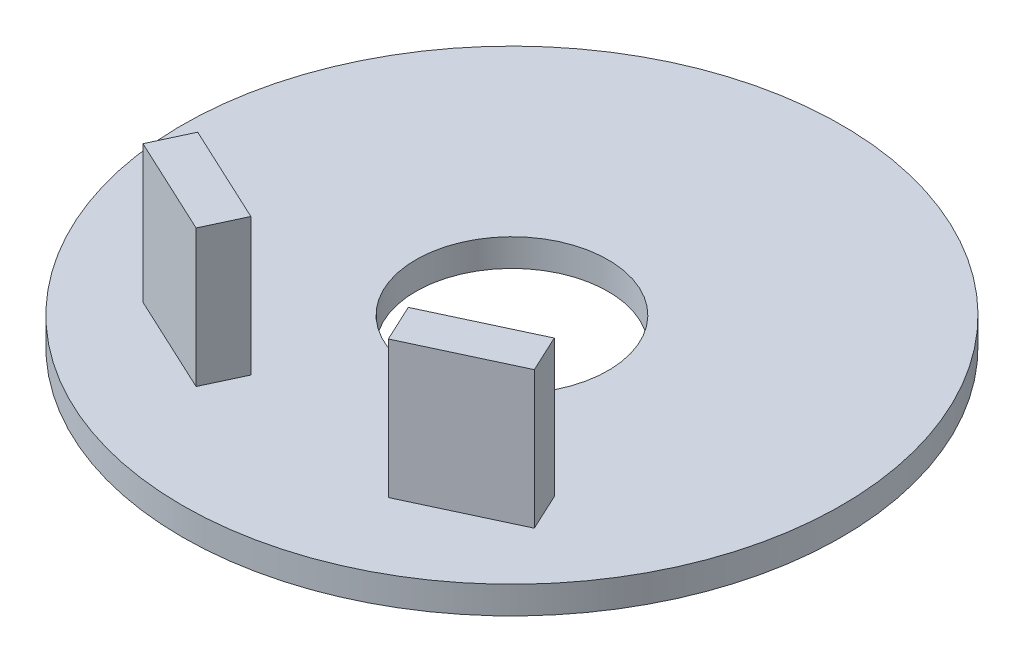
SolidWorks part; units mm, degrees
ref_plane "Plano frontal" through (0, 0, 0) normal (0, 0, 1) x (1, 0, 0)
ref_plane "Plano superior" through (0, 0, 0) normal (0, 1, 0) x (1, 0, 0)
ref_plane "Plano direito" through (0, 0, 0) normal (1, 0, 0) x (0, 0, -1)
sketch "Sketch1" plane through (0, 0, 0) normal (0, 1, 0) x (1, 0, 0)
  circle A0 centre (0, 0) radius 12
  circle A1 centre (0, 0) radius 3.5
  dimension "D1" = 24
  dimension "D2" = 7
extrude "Boss-Extrude1" add sketch "Sketch1" along normal mid plane 1
sketch "Sketch2" plane through (0, -0.5, 0) normal (0, 1, 0) x (1, 0, 0)
  line L1 (-7, 14) -> (7, 14)
  line L2 (-7, 14) -> (-7, 8)
  line L3 (-7, 8) -> (7, 8)
  line L4 (7, 14) -> (7, 8)
  circle A0 centre (0, 0) radius 12 construction
  point P4 (0, 8)
  dimension "D3" = 2
  dimension "D1" = 6
  dimension "D2" = 14
extrude "Boss-Extrude2" [suppressed] add sketch "Sketch2" against normal blind 5
sketch "Sketch3" [suppressed] plane through (0, 0, -14) normal (0, 0, -1) x (-1, 0, 0)
  line L10 (6.5, -1) -> (-6.5, -1)
  line L11 (-6.5, -1) -> (-6.5, -5)
  line L12 (-6.5, -5) -> (6.5, -5)
  line L13 (6.5, -5) -> (6.5, -1)
  line L18 (7, -0.5) -> (-7, -0.5)
  line L19 (-7, -0.5) -> (-7, -5.5)
  line L20 (-7, -5.5) -> (7, -5.5)
  line L21 (7, -5.5) -> (7, -0.5)
  line L22 (7, -0.5) -> (-7, -0.5) construction
  line L23 (-7, -0.5) -> (-7, -5.5) construction
  line L24 (-7, -5.5) -> (7, -5.5) construction
  line L25 (7, -5.5) -> (7, -0.5) construction
  dimension "D1" = 0
  dimension "D2" = 0.5
extrude "Cut-Extrude1" [suppressed] cut sketch "Sketch3" against normal offset from surface (5 mm away) 1
sketch "Sketch4" [suppressed] plane through (0, -5.5, 0) normal (0, -1, 0) x (-1, 0, 0)
  line L0 (-7, 14) -> (7, 14) construction
  line L1 (4, 14) -> (-4, 14)
  line L2 (4, 14) -> (4, 9)
  line L3 (4, 9) -> (-4, 9)
  line L4 (-4, 14) -> (-4, 9)
  line L5 (7, 14) -> (7, 8) construction
  point P13 (0, 9)
  dimension "D1" = 3
  dimension "D2" = 5
extrude "Cut-Extrude2" [suppressed] cut sketch "Sketch4" against normal up to surface (0.5 mm away)
sketch "Sketch5" plane through (0, 0.5, 0) normal (0, 1, 0) x (1, 0, 0)
  line L0 (-8.9443, -8) -> (8.9443, -8) construction
  line L1 (-6.4913, -4.9501) -> (-2.8661, -6.6405)
  line L2 (-2.8661, -6.6405) -> (-3.5, -8)
  line L3 (-3.5, -8) -> (-7.1252, -6.3095)
  line L4 (-7.1252, -6.3095) -> (-6.4913, -4.9501)
  line L5 (0, -6.05) -> (0, 6.05) construction
  line L6 (7.1252, -6.3095) -> (6.4913, -4.9501)
  line L7 (3.5, -8) -> (7.1252, -6.3095)
  line L8 (2.8661, -6.6405) -> (3.5, -8)
  line L9 (6.4913, -4.9501) -> (2.8661, -6.6405)
  circle A0 centre (0, 0) radius 12 construction
  dimension "D1" = 4
  dimension "D2" = 4
  dimension "D3" = 1.5
  dimension "D4" = 7
  dimension "D5" = 25
extrude "Boss-Extrude3" add sketch "Sketch5" along normal blind 5
